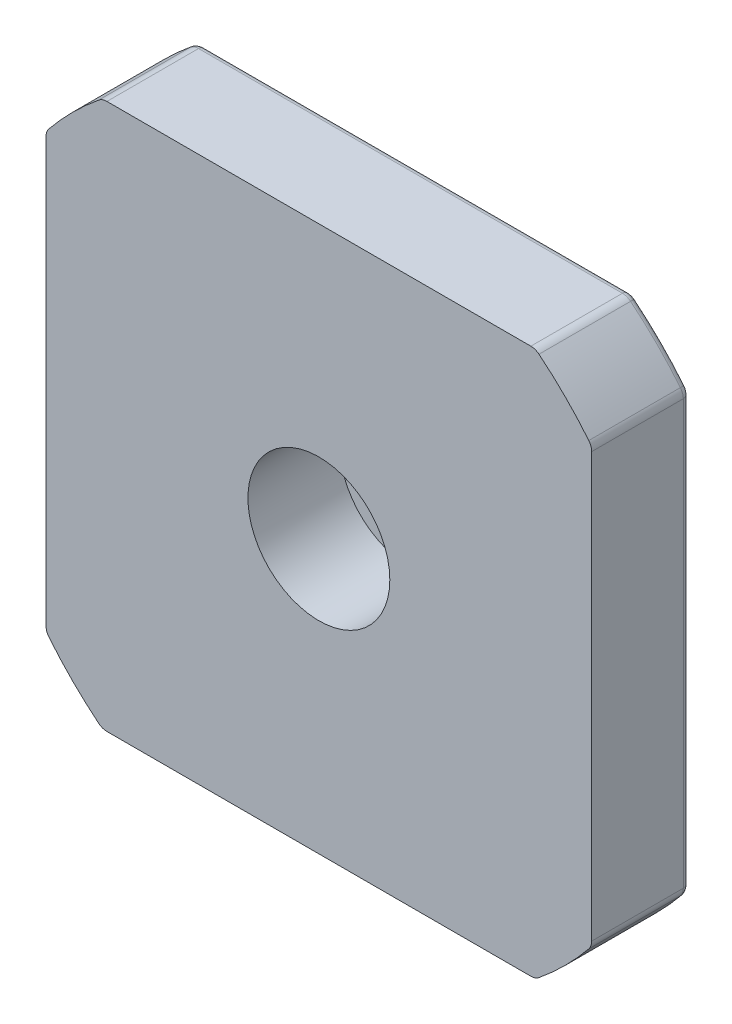
SolidWorks part; units mm, degrees
material "Acero aleado"
ref_plane "Alzado" through (0, 0, 0) normal (0, 0, 1) x (1, 0, 0)
ref_plane "Planta" through (0, 0, 0) normal (0, 1, 0) x (1, 0, 0)
ref_plane "Vista lateral" through (0, 0, 0) normal (1, 0, 0) x (0, 0, -1)
sketch "Croquis1" plane through (0, 0, 0) normal (0, 0, 1) x (1, 0, 0)
  line L0 (21.15, -21.15) -> (-21.15, -21.15)
  line L1 (21.15, 21.15) -> (-21.15, 21.15)
  line L2 (-21.15, 21.15) -> (-21.15, -21.15)
  line L4 (21.15, 21.15) -> (21.15, -21.15)
  line L5 (-21.15, 21.15) -> (21.15, -21.15) construction
  line L6 (-21.15, -21.15) -> (21.15, 21.15) construction
  point P0 (0, 0)
  dimension "D1" = 42.3
  dimension "D2" = 42.3
extrude "Saliente-Extruir1" add sketch "Croquis1" along normal blind 7.6
sketch "Sketch1" plane through (0, 0, 0) normal (0, 0, -1) x (-1, 0, 0)
  circle A0 centre (0, 0) radius 27
  circle A1 centre (0, 0) radius 29.9106
  dimension "D1" = 54
extrude "Cut-Extrude1" cut sketch "Sketch1" against normal through all
sketch "Croquis3" plane through (0, 0, 0) normal (0, 0, -1) x (-1, 0, 0)
  circle A0 centre (0, 0) radius 11
  circle A1 centre (0, 0) radius 8.5
  dimension "D1" = 22
  dimension "D2" = 2.5
extrude "Saliente-Extruir2" add sketch "Croquis3" along normal blind 2
sketch "Croquis4" plane through (0, 0, -2) normal (0, 0, -1) x (-1, 0, 0)
  circle A0 centre (0, 0) radius 4.5
  dimension "D1" = 9
extrude "Cortar-Extruir2" cut sketch "Croquis4" against normal blind 7
sketch "Croquis5" plane through (0, 0, 5) normal (0, 0, -1) x (-1, 0, 0)
  circle A0 centre (0, 0) radius 2.5
  dimension "D1" = 5
extrude "Cortar-Extruir3" cut sketch "Croquis5" against normal blind 7
sketch "Croquis6" plane through (0, 0, 0) normal (0, 0, -1) x (-1, 0, 0)
  circle A0 centre (-15.5, 15.5) radius 1.5
  circle A1 centre (15.5, 15.5) radius 1.5
  circle A2 centre (15.5, -15.5) radius 1.5
  circle A3 centre (-15.5, -15.5) radius 1.5
  point P12 (0, 0)
  dimension "D1" = 3
  dimension "D2" = 15.5
  dimension "D3" = 15.5
  dimension "D5" = 15.5
  dimension "D6" = 15.5
  dimension "D4" = 4
extrude "Cortar-Extruir4" cut sketch "Croquis6" against normal blind 4.5
sketch "Sketch2" plane through (0, 0, 7.6) normal (0, 0, 1) x (1, 0, 0)
  circle A0 centre (0, 0) radius 5.5
  dimension "D1" = 11
extrude "Cut-Extrude2" cut sketch "Sketch2" against normal offset from surface (7.1 mm away) 0.5 up to face at (-4.5, 0, 0)
sketch "Sketch3" plane through (0, 0, 0) normal (0, 0, -1) x (-1, 0, 0)
  circle A0 centre (0, 0) radius 16.5
  circle A1 centre (0, 0) radius 11.5
  circle A2 centre (0, 0) radius 11 construction
  dimension "D1" = 33
  dimension "D2" = 0.5
extrude "Cut-Extrude3" cut sketch "Sketch3" against normal blind 0.1
fillet "Fillet1" radius 1 8 edges at (-16.7833, 21.15, 3.8) (16.7833, 21.15, 3.8) (21.15, 16.7833, 3.8) (21.15, -16.7833, 3.8) (16.7833, -21.15, 3.8) (-16.7833, -21.15, 3.8) (-21.15, -16.7833, 3.8) (-21.15, 16.7833, 3.8)
fillet "Fillet2" radius 0.5 16 edges at (-21.0921, 16.7664, 0) (-21.15, 0, 0) (-21.0921, -16.7664, 0) (-19.0919, -19.0919, 0) (-16.7664, -21.0921, 0) (0, -21.15, 0) (16.7664, -21.0921, 0) (19.0919, -19.0919, 0) (21.0921, -16.7664, 0) (21.15, 0, 0) (21.0921, 16.7664, 0) (19.0919, 19.0919, 0) (16.7664, 21.0921, 0) (0, 21.15, 0) (-16.7664, 21.0921, 0) (-19.0919, 19.0919, 0)
chamfer "Chamfer1" distance 0.5 angle 45 1 edges at (-11, 0, -2)
